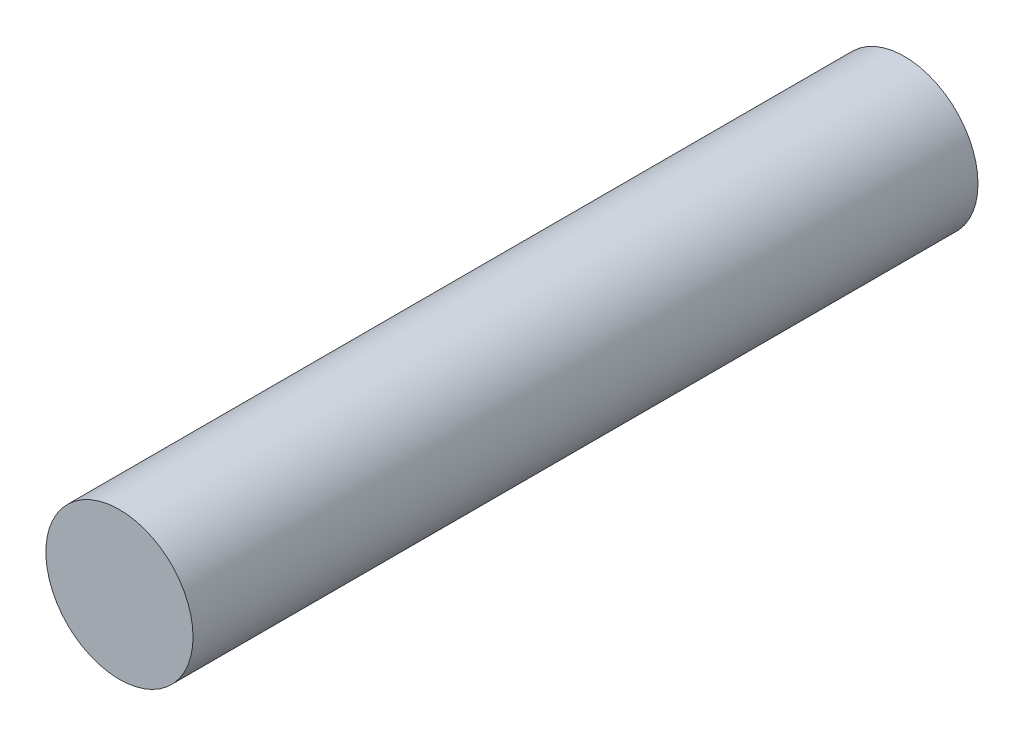
SolidWorks part; units mm, degrees
ref_plane "正面" through (0, 0, 0) normal (0, 0, 1) x (1, 0, 0)
ref_plane "平面" through (0, 0, 0) normal (0, 1, 0) x (1, 0, 0)
ref_plane "右側面" through (0, 0, 0) normal (1, 0, 0) x (0, 0, -1)
sketch "ｽｹｯﾁ1" plane through (0, 0, 0) normal (0, 0, 1) x (1, 0, 0)
  circle A0 centre (0, 0) radius 1.5
  dimension "D1" = 3
extrude "ﾎﾞｽ - 押し出し1" add sketch "ｽｹｯﾁ1" along normal blind 16
